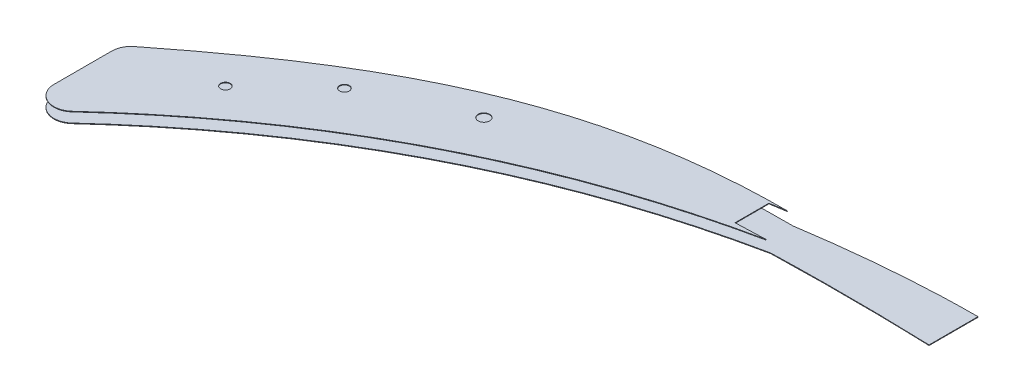
SolidWorks part; units mm, degrees
material "Thornel Mat VMA"
ref_plane "Płaszczyzna XY" through (0, 0, 0) normal (0, 0, 1) x (1, 0, 0)
ref_plane "Płaszczyzna XZ" through (0, 0, 0) normal (0, 1, 0) x (1, 0, 0)
ref_plane "Płaszczyzna YZ" through (0, 0, 0) normal (1, 0, 0) x (0, 0, -1)
sketch "Szkic1" plane through (0, 295, 0) normal (0, -1, 0) x (1, 0, 0)
  line L5 (-77.1875, 238.3715) -> (-77.1875, 263.7875)
  line L6 (-416.2266, 379.1412) -> (-416.2266, 349.1234)
  line L9 (-77.1875, 238.3715) -> (-77.1875, 263.7875)
  line L10 (-416.2266, 379.1412) -> (-416.2266, 349.1234)
  arc A2 (-399.4517, 386.4964) -> (-416.2266, 379.1412) centre (-406.2266, 379.1412) ccw
  arc A3 (-416.2266, 349.1234) -> (-412.4215, 341.2733) centre (-406.2266, 349.1234) ccw
  arc A4 (-399.4517, 386.4964) -> (-416.2266, 379.1412) centre (-406.2266, 379.1412) ccw
  arc A5 (-416.2266, 349.1234) -> (-412.4215, 341.2733) centre (-406.2266, 349.1234) ccw
  spline S10 degree 3 poles (2575.9742, -920.3536) (-1289.7119, 1236.5689) (-747.8511, 314.9564) (-136.5577, 241.6991) (-129.1651, 240.941) (-114.3549, 239.6992) (-106.9373, 239.215) (-95.7901, 238.7173) (-92.0701, 238.5898) (233.3481, 231.0513) (560.3619, 531.5624) (924.6836, 2993.4738) knots -20.204794 -20.204794 -20.204794 -20.204794 0.25 0.25 0.5 0.5 0.75 0.75 0.875 0.875 11.684459 11.684459 11.684459 11.684459 only from (-166.0462, 245.6107) to (-77.1875, 238.3715)
  spline S11 degree 3 poles (1124.7282, 2750.187) (1129.0827, 717.9913) (504.1406, 264.4534) (-1174.9046, 260.5843) (-2247.3512, 1537.2252) (-7.5925, -1125.283) knots -22.140765 -22.140765 -22.140765 -22.140765 0.5 0.5 38.920289 38.920289 38.920289 38.920289 only from (-77.1875, 263.7875) to (-159.6784, 263.5621)
  spline S12 degree 3 poles (2044.102, 2156.3643) (128.3636, -934.4192) (-1539.1906, -50.8389) (-138.9596, 3278.9306) knots -4.770164 -4.770164 -4.770164 -4.770164 5.654576 5.654576 5.654576 5.654576 only from (-159.6784, 263.5621) to (-399.4517, 386.4964)
  spline S13 degree 3 poles (-3268.9979, 1039.04) (1404.9754, 1043.2985) (-2161.306, -1079.9395) (2502.9409, 1602.6516) knots -3.172382 -3.172382 -3.172382 -3.172382 3.595344 3.595344 3.595344 3.595344 only from (-412.4215, 341.2733) to (-166.0462, 245.6107)
  spline S18 degree 3 poles (-166.0462, 245.6107) (-158.6916, 244.4796) (-151.3198, 243.4682) (-136.5577, 241.6991) (-129.1651, 240.941) (-114.3549, 239.6992) (-106.9373, 239.215) (-95.7901, 238.7173) (-92.0701, 238.5898) (-84.6299, 238.4175) (-80.909, 238.3725) (-77.1875, 238.3715) knots 0 0 0 0 0.25 0.25 0.5 0.5 0.75 0.75 0.875 0.875 1 1 1 1
  spline S19 degree 3 poles (-77.1875, 263.7875) (-90.9319, 263.3027) (-104.682, 263.0505) (-132.1798, 262.9871) (-145.9314, 263.1721) (-159.6784, 263.5621) knots 0 0 0 0 0.5 0.5 1 1 1 1
  spline S20 degree 3 poles (-159.6784, 263.5621) (-250.7067, 282.3303) (-331.1663, 323.5984) (-399.4517, 386.4964) knots 0 0 0 0 0.864061 0.864061 0.864061 0.864061
  spline S21 degree 3 poles (-412.4215, 341.2733) (-337.5624, 282.199) (-268.6848, 244.735) (-166.0462, 245.6107) knots 0.076862 0.076862 0.076862 0.076862 0.98459 0.98459 0.98459 0.98459
  dimension "D1" = 0
extrude "Dodanie-wyciągnięcie1" add sketch "Szkic1" along normal blind 0.3
sketch "Szkic2" plane through (0, 300, 0) normal (0, 1, 0) x (1, 0, 0)
  line L2 (-177.1875, -264.5091) -> (-177.1875, -246.9458)
  line L3 (-416.2266, -349.1234) -> (-416.2266, -379.1412)
  line L4 (-177.1875, -264.5091) -> (-177.1875, -246.9458)
  line L5 (-416.2266, -349.1234) -> (-416.2266, -379.1412)
  arc A2 (-168.7665, -245.5964) -> (-177.1875, -246.9458) centre (-62.2203, -937.4497) ccw
  arc A3 (-412.4215, -341.2733) -> (-416.2266, -349.1234) centre (-406.2266, -349.1234) ccw
  arc A4 (-416.2266, -379.1412) -> (-399.4517, -386.4964) centre (-406.2266, -379.1412) ccw
  arc A5 (-168.7665, -245.5964) -> (-177.1875, -246.9458) centre (-62.2203, -937.4497) ccw
  arc A6 (-412.4215, -341.2733) -> (-416.2266, -349.1234) centre (-406.2266, -349.1234) ccw
  arc A7 (-416.2266, -379.1412) -> (-399.4517, -386.4964) centre (-406.2266, -379.1412) ccw
  spline S4 degree 3 poles (1763.6413, -2392.2313) (962.0259, -549.7473) (381.0974, -244.4375) (-748.6502, -285.0211) (-1297.5572, -665.3581) (-1918.3224, -2536.9777) knots -6.77928 -6.77928 -6.77928 -6.77928 0.480355 0.511605 8.11549 8.11549 8.11549 8.11549 only from (-161.6097, -263.9641) to (-177.1875, -264.5091)
  spline S5 degree 3 poles (2500.739, -1601.3852) (-2160.1917, 1079.2758) (1404.2521, -1043.3052) (-3269.0223, -1039.04) knots -2.532826 -2.532826 -2.532826 -2.532826 4.233847 4.233847 4.233847 4.233847 only from (-168.7665, -245.5964) to (-412.4215, -341.2733)
  spline S6 degree 3 poles (-138.9662, -3278.915) (-1538.9629, 50.3126) (127.8367, 934.1335) (2043.1887, -2154.8912) knots -4.790499 -4.790499 -4.790499 -4.790499 5.632568 5.632568 5.632568 5.632568 only from (-399.4517, -386.4964) to (-161.6097, -263.9641)
  spline S7 degree 3 poles (-161.6097, -263.9641) (-163.4618, -264.0186) (-167.6847, -264.1512) (-172.8769, -264.3378) (-176.217, -264.4698) (-177.1875, -264.5091) knots 0.45595 0.45595 0.45595 0.45595 0.480355 0.511605 0.524405 0.524405 0.524405 0.524405
  spline S8 degree 3 poles (-168.7665, -245.5964) (-269.9058, -245.4006) (-338.2257, -282.7224) (-412.4215, -341.2733) knots 0.084905 0.084905 0.084905 0.084905 0.98459 0.98459 0.98459 0.98459
  spline S9 degree 3 poles (-399.4517, -386.4964) (-331.6497, -324.0436) (-251.8451, -282.9156) (-161.6097, -263.9641) knots 0 0 0 0 0.857945 0.857945 0.857945 0.857945
  dimension "D1" = 0
extrude "Dodanie-wyciągnięcie2" add sketch "Szkic2" along normal blind 0.3 separate body
sketch "Szkic3" plane through (0, 300.3, 0) normal (0, 1, 0) x (1, 0, 0)
  circle A0 centre (-370.9569, -335.3671) radius 2.5 construction
  circle A1 centre (-339.083, -305.4298) radius 2.5 construction
  circle A2 centre (-289.6871, -282.4241) radius 3 construction
  circle A3 centre (-370.9569, -335.3671) radius 2.5
  circle A4 centre (-339.083, -305.4298) radius 2.5
  circle A5 centre (-289.6871, -282.4241) radius 3
extrude "Wytnij-wyciągnięcie1" cut sketch "Szkic3" against normal blind 12
